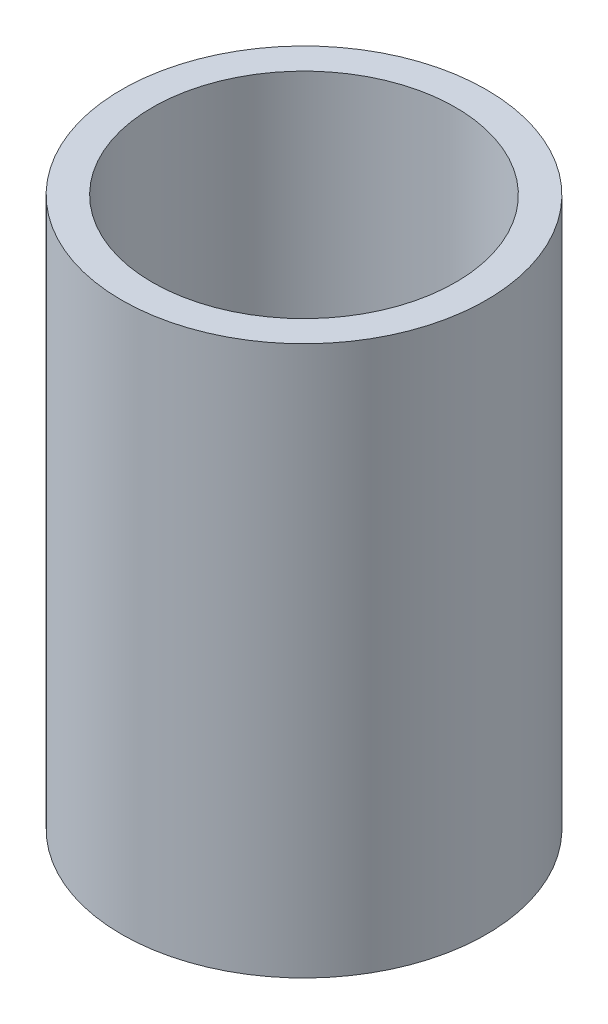
SolidWorks part; units mm, degrees
material "6061 Alloy"
ref_plane "Front Plane" through (0, 0, 0) normal (0, 0, 1) x (1, 0, 0)
ref_plane "Top Plane" through (0, 0, 0) normal (0, 1, 0) x (1, 0, 0)
ref_plane "Right Plane" through (0, 0, 0) normal (1, 0, 0) x (0, 0, -1)
sketch "Sketch1" plane through (0, 0, 0) normal (0, 1, 0) x (1, 0, 0)
  circle A0 centre (0, 0) radius 21.082
  circle A1 centre (0, 0) radius 17.526
  dimension "D1" = 42.164
  dimension "D2" = 3.556
extrude "Boss-Extrude1" add sketch "Sketch1" along normal blind 63.5
